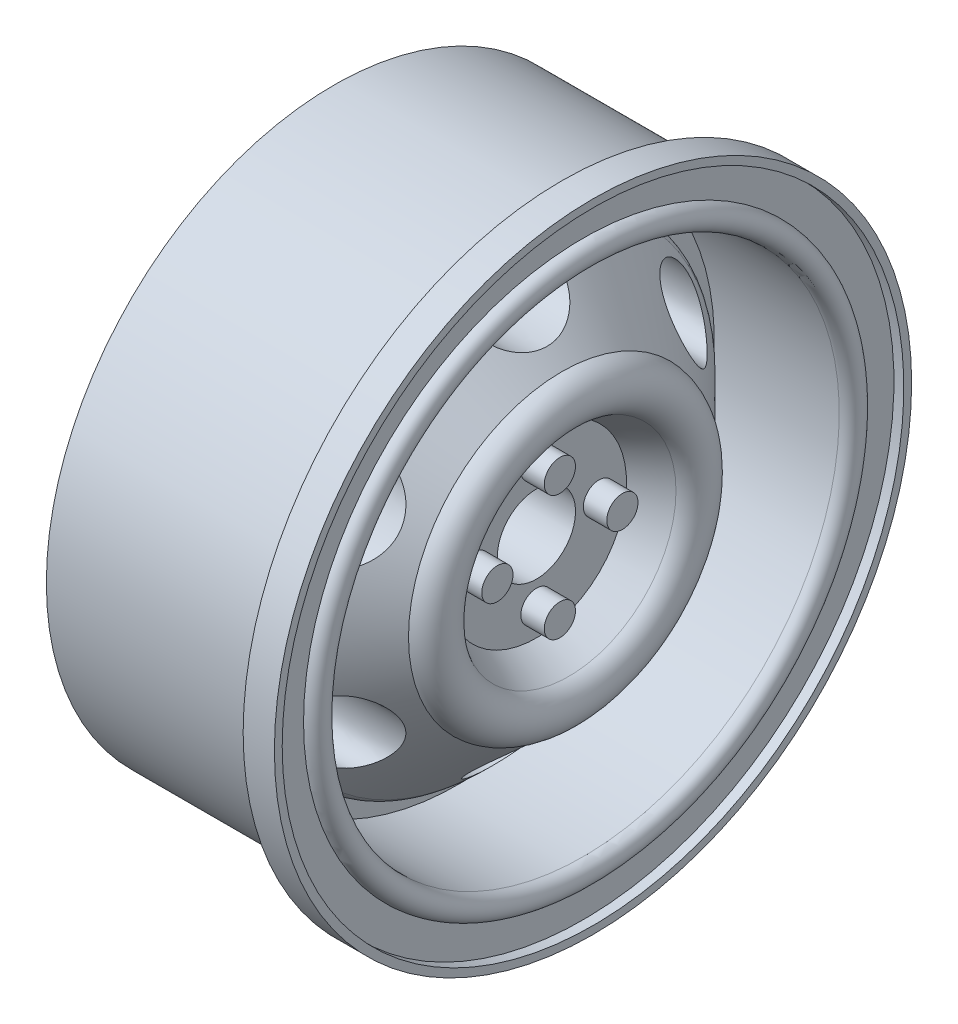
SolidWorks part; units mm, degrees
ref_plane "Front Plane" through (0, 0, 0) normal (0, 0, 1) x (1, 0, 0)
ref_plane "Top Plane" through (0, 0, 0) normal (0, 1, 0) x (1, 0, 0)
ref_plane "Right Plane" through (0, 0, 0) normal (1, 0, 0) x (0, 0, -1)
sketch "Sketch1" plane through (0, 0, 0) normal (0, 1, 0) x (1, 0, 0)
  line L0 (-27.75, 0) -> (38.25, 0) construction
  line L1 (15.9658, 17.9) -> (15.9658, 19.9)
  line L2 (0, 18.4) -> (14.6, 18.4)
  line L4 (4.9658, 2.5) -> (11.3174, 2.5)
  line L6 (16.1, 20.4) -> (14.6, 20.4)
  line L7 (14.6, 20.4) -> (14.6, 18.4)
  line L8 (16.1, 20.4) -> (16.6, 20.4)
  line L9 (16.6, 20.4) -> (16.6, 19.9)
  line L10 (16.6, 19.9) -> (15.9658, 19.9)
  line L11 (15.9658, 16.4) -> (7.9658, 16.4)
  line L12 (7.9658, 16.4) -> (7.9658, 14.9)
  line L19 (0, 18.4) -> (15.9658, 18.4) construction
  line L22 (0, 18.4) -> (0, 15.4)
  line L23 (0, 15.4) -> (4.9658, 15.4)
  line L25 (7.3, 18.4) -> (7.3, 0) construction
  line L26 (4.9658, 7.35) -> (4.9658, 2.5)
  line L27 (4.9658, 15.4) -> (4.9658, 10.4)
  line L29 (4.9658, 10.4) -> (4.9658, 7.35)
  line L30 (7.9658, 14.9) -> (9.5138, 14.9)
  line L34 (15.9658, 16.4) -> (15.9658, 0) construction
  line L35 (9.5138, 14.9) -> (14.6, 9.8138)
  line L38 (15.049, 6.8635) -> (12.9786, 5.7646)
  line L39 (12.9786, 5.7646) -> (12.9786, 2.5)
  line L40 (12.9786, 2.5) -> (11.3174, 2.5)
  arc A0 (15.9658, 16.4) -> (15.9658, 17.9) centre (15.9658, 17.15) ccw
  arc A5 (14.6, 9.8138) -> (15.049, 6.8635) centre (14.418, 8.2767) cw
  point P41 (12.3593, 9.9719)
  point P46 (13.269, 5.5)
  dimension "D7" = 1.5
  dimension "D2" = 36.8
  dimension "D3" = 5
  dimension "D4" = 1.5
  dimension "D5" = 1.5
  dimension "D6" = 0.5
  dimension "D8" = 2
  dimension "D9" = 8
  dimension "D10" = 14.6
  dimension "D11" = 6.6342
  dimension "D12" = 9.6342
  dimension "D13" = 3
  dimension "D14" = 3
  dimension "D15" = 5
  dimension "D17" = 0.5
revolve "Revolve1" add sketch "Sketch1" angle 360 about L0
sketch "Sketch5" plane through (4.9658, 0, 0) normal (-1, 0, 0) x (0, 0, 1)
  circle A0 centre (0, 0) radius 5.75
  circle A1 centre (0, 0) radius 7.5
  dimension "D1" = 11.5
  dimension "D2" = 15
extrude "Boss-Extrude2" add sketch "Sketch5" along normal blind 5
sketch "Sketch6" plane through (12.9786, 0, 0) normal (1, 0, 0) x (0, 0, -1)
  circle A0 centre (0, 0) radius 4.0018 construction
  circle A1 centre (0, 4.0018) radius 1
  circle A2 centre (4.0018, 0) radius 1
  circle A3 centre (0, -4.0018) radius 1
  circle A4 centre (-4.0018, 0) radius 1
  point P14 (0, 0)
  dimension "D1" = 2
  dimension "D2" = 4
extrude "Boss-Extrude3" add sketch "Sketch6" along normal blind 1.5
sketch "Sketch7" plane through (12.9786, 0, 0) normal (1, 0, 0) x (0, 0, -1)
  circle A2 centre (0, 0) radius 12.5 construction
  ellipse E0 centre (0, 12.5) end of major axis (3, 12.5) minor radius 1.75
  ellipse E1 centre (10.8253, 6.25) end of major axis (9.3253, 8.8481) minor radius 1.75
  ellipse E2 centre (10.8253, -6.25) end of major axis (12.3253, -3.6519) minor radius 1.75
  ellipse E3 centre (0, -12.5) end of major axis (3, -12.5) minor radius 1.75
  ellipse E4 centre (-10.8253, -6.25) end of major axis (-9.3253, -8.8481) minor radius 1.75
  ellipse E5 centre (-10.8253, 6.25) end of major axis (-12.3253, 3.6519) minor radius 1.75
  point P42 (-0.0002, 8.3595)
  point P44 (0, 0)
  dimension "D1" = 25
  dimension "D2" = 6
  dimension "D3" = 3.5
  dimension "D4" = 6
extrude "Cut-Extrude1" cut sketch "Sketch7" against normal through all both and the other way through all
fillet "Fillet1" radius 1 1 edges at (9.5138, 0, 14.9)
